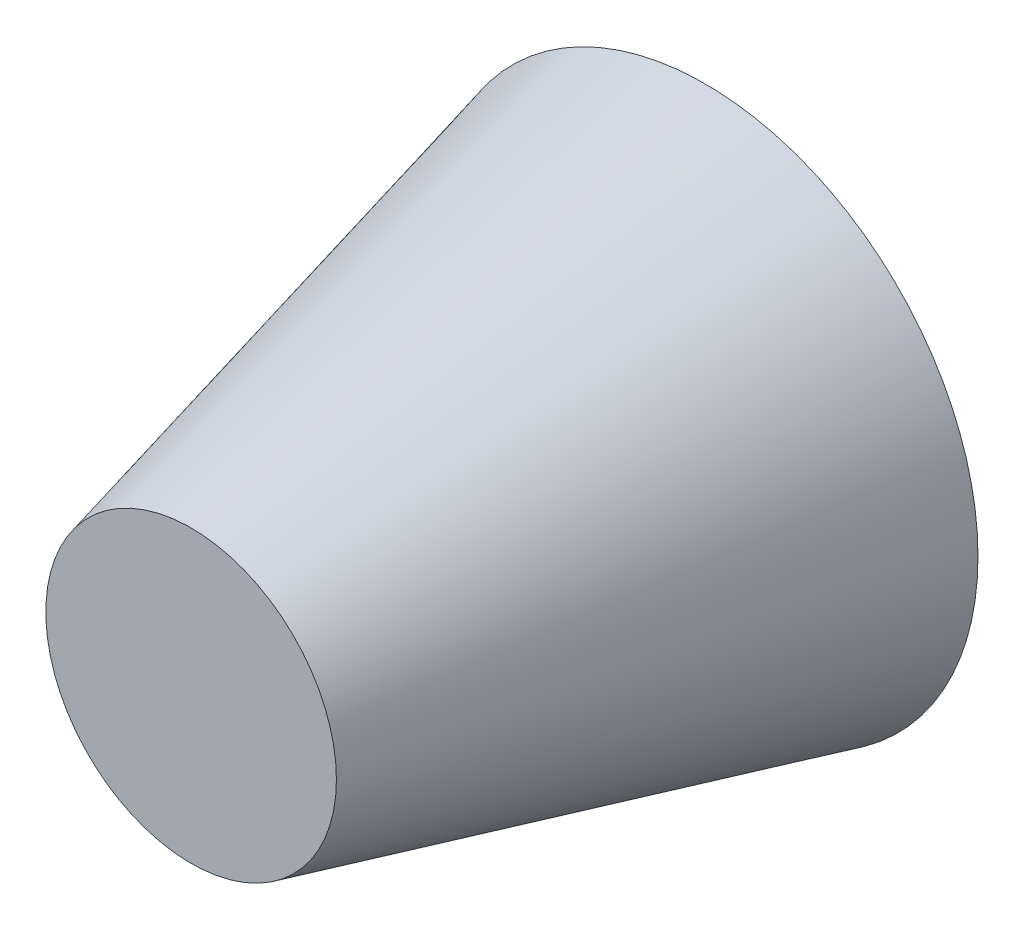
SolidWorks part; units mm, degrees
ref_plane "Front Plane" through (0, 0, 0) normal (0, 0, 1) x (1, 0, 0)
ref_plane "Top Plane" through (0, 0, 0) normal (0, 1, 0) x (1, 0, 0)
ref_plane "Right Plane" through (0, 0, 0) normal (1, 0, 0) x (0, 0, -1)
sketch "Sketch2" plane through (0, 0, 0) normal (0, 0, 1) x (1, 0, 0)
  circle A0 centre (0, 0) radius 6.1
ref_plane "Plane1" through (0, 0, 11.5) normal (0, 0, 1) x (1, 0, 0)
sketch "Sketch3" plane through (0, 0, 11.5) normal (0, 0, 1) x (1, 0, 0)
  circle A0 centre (0, 0) radius 3.25
loft "Loft1" add profiles "Sketch3", "Sketch2"
